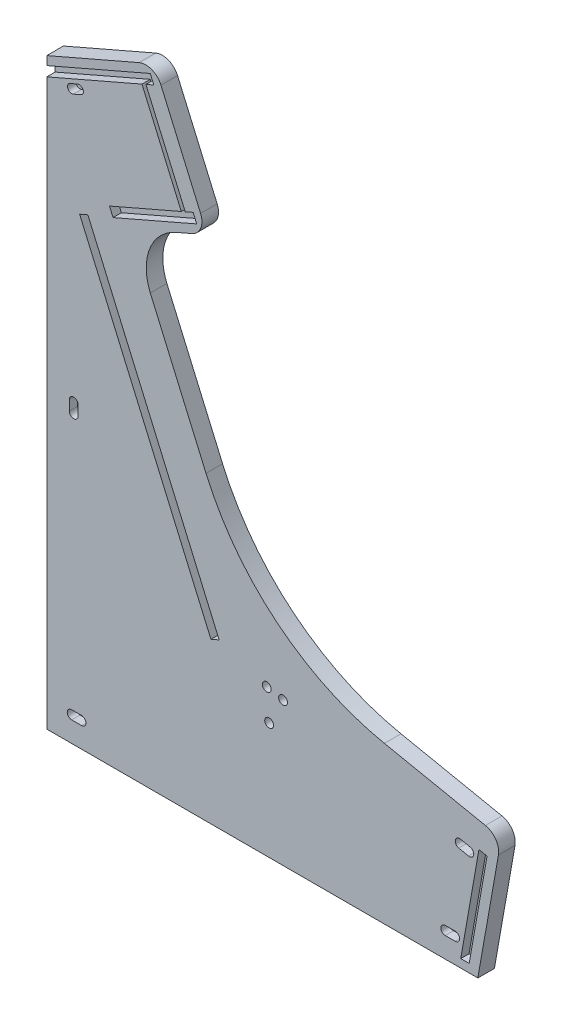
SolidWorks part; units mm, degrees
ref_plane "Alzado" through (0, 0, 0) normal (0, 0, 1) x (1, 0, 0)
ref_plane "Planta" through (0, 0, 0) normal (0, 1, 0) x (1, 0, 0)
ref_plane "Vista lateral" through (0, 0, 0) normal (1, 0, 0) x (0, 0, -1)
sketch "Croquis1" plane through (0, 0, 0) normal (0, 0, 1) x (1, 0, 0)
  line L8 (0, 0) -> (260, 0)
  line L9 (260, 0) -> (274.1062, 80)
  line L10 (274.1062, 80) -> (127.1368, 110)
  line L11 (127.1368, 110) -> (50.509, 286.5431)
  line L12 (50.509, 286.5431) -> (96.7519, 306.6146)
  line L13 (96.7519, 306.6146) -> (64.8993, 380)
  line L14 (64.8993, 380) -> (0, 351.8307)
  line L15 (0, 351.8307) -> (0, 0)
  dimension "D1" = 380
  dimension "D2" = 260
  dimension "D3" = 80
  dimension "D4" = 150
  dimension "D5" = 100
  dimension "D6" = 110
  dimension "D7" = 125
  dimension "D8" = 80
extrude "Saliente-Extruir1" add sketch "Croquis1" along normal blind 10
fillet "Redondeo1" radius 30 1 edges at (50.509, 286.5431, 5)
fillet "Redondeo2" radius 150 1 edges at (127.1368, 110, 5)
fillet "Redondeo3" radius 10 3 edges at (64.8993, 380, 5) (96.7519, 306.6146, 5) (274.1062, 80, 5)
sketch "Croquis2" plane through (0, 0, 10) normal (0, 0, 1) x (1, 0, 0)
  line L0 (39.907, 287.3921) -> (90.176, 309.2111) construction
  line L8 (90.176, 309.2111) -> (88.1852, 313.7977) construction
  line L10 (37.9163, 291.9786) -> (88.1852, 313.7977) construction
  line L11 (0, 340.9294) -> (45.3064, 360.5944) construction
  line L18 (64.2958, 368.8367) -> (62.305, 373.4233) construction
  line L21 (0, 346.3801) -> (62.305, 373.4233) construction
  line L22 (45.3064, 360.5944) -> (64.2958, 368.8367) construction
  line L23 (55.7261, 376.0184) -> (87.5787, 302.6331) construction
  line L24 (68.8809, 370.8268) -> (64.2958, 368.8367) construction
  line L25 (92.7703, 315.7878) -> (88.1852, 313.7977) construction
  line L26 (0, 351.8307) -> (55.7261, 376.0184) construction
  line L30 (39.9867, 287.2086) -> (90.4391, 309.1073)
  line L31 (90.4391, 309.1073) -> (88.2891, 314.0608)
  line L34 (0, 346.5981) -> (0, 340.7114)
  line L35 (37.8366, 292.1621) -> (81.1325, 310.9545)
  line L36 (0, 340.7114) -> (57.4023, 365.6266)
  line L37 (64.5589, 368.7329) -> (62.4088, 373.6864)
  line L38 (0, 346.5981) -> (62.4088, 373.6864)
  line L39 (92.7703, 315.7878) -> (68.8809, 370.8268) construction
  line L40 (39.9867, 287.2086) -> (37.8366, 292.1621)
  line L41 (57.4023, 365.6266) -> (81.1325, 310.9545)
  line L44 (59.7873, 366.6618) -> (83.5175, 311.9897)
  line L45 (59.7873, 366.6618) -> (64.5589, 368.7329)
  line L46 (83.5175, 311.9897) -> (88.2891, 314.0608)
  line L48 (57.3227, 365.81) -> (81.2121, 310.771) construction
  line L49 (59.7077, 366.8453) -> (83.5971, 311.8062) construction
  arc A1 (92.7703, 315.7878) -> (87.5787, 302.6331) centre (83.5971, 311.8062) cw construction
  arc A4 (55.7261, 376.0184) -> (68.8809, 370.8268) centre (59.7077, 366.8453) cw construction
  point P18 (53.3411, 374.9832)
  point P20 (85.1937, 301.5978)
  point P22 (-1.9908, 280.3259)
  point P25 (79.1417, 315.5411)
  dimension "D1" = 10
  dimension "D2" = 55
  dimension "D3" = 4.9984
extrude "Cortar-Extruir1" cut sketch "Croquis2" against normal blind 5
sketch "Croquis3" [suppressed] plane through (0, 0, 0) normal (0, 0, -1) x (-1, 0, 0)
  line L0 (0, 351.8307) -> (-55.7261, 376.0184) construction
  line L10 (0, 346.5981) -> (-62.4088, 373.6864)
  line L12 (-64.5589, 368.7329) -> (-62.4088, 373.6864)
  line L19 (0, 340.7114) -> (-57.4023, 365.6266)
  line L28 (-37.8366, 292.1621) -> (-81.1325, 310.9545)
  line L29 (-92.7703, 315.7878) -> (-88.1852, 313.7977) construction
  line L30 (-47.6793, 361.4064) -> (-64.5589, 368.7329) construction
  line L31 (-68.8809, 370.8268) -> (-64.2958, 368.8367) construction
  line L32 (-55.7261, 376.0184) -> (-87.5787, 302.6331) construction
  line L34 (-45.3064, 360.5944) -> (-64.2958, 368.8367) construction
  line L35 (0, 346.5981) -> (0, 340.7114)
  line L36 (0, 346.3801) -> (-62.305, 373.4233) construction
  line L37 (-64.2958, 368.8367) -> (-62.305, 373.4233) construction
  line L38 (0, 340.9294) -> (-45.3064, 360.5944) construction
  line L39 (-37.9163, 291.9786) -> (-88.1852, 313.7977) construction
  line L40 (-90.176, 309.2111) -> (-88.1852, 313.7977) construction
  line L42 (-39.907, 287.3921) -> (-90.176, 309.2111) construction
  line L45 (-90.4391, 309.1073) -> (-88.2891, 314.0608)
  line L46 (-39.9867, 287.2086) -> (-90.4391, 309.1073)
  line L50 (-71.4095, 306.7343) -> (-88.2891, 314.0608) construction
  line L51 (0.0796, 346.5635) -> (-62.4088, 373.6864) construction
  line L52 (-0.0796, 269.8871) -> (-90.4391, 309.1073) construction
  line L53 (-47.5997, 361.5898) -> (-64.2958, 368.8367) construction
  line L54 (-71.4891, 306.5508) -> (-88.1852, 313.7977) construction
  line L55 (-90.176, 309.2111) -> (-88.1852, 313.7977) construction
  line L56 (-57.4023, 365.6266) -> (-81.1325, 310.9545)
  line L57 (-59.7873, 366.6618) -> (-64.5589, 368.7329)
  line L58 (-53.3411, 374.9832) -> (-85.1937, 301.5978) construction
  line L59 (-83.5175, 311.9897) -> (-88.2891, 314.0608)
  line L60 (-83.5175, 311.9897) -> (-59.7873, 366.6618)
  line L61 (-39.9867, 287.2086) -> (-37.8366, 292.1621)
  line L63 (0, 270.0706) -> (-90.176, 309.2111) construction
  arc A0 (-55.7261, 376.0184) -> (-68.8809, 370.8268) centre (-59.7077, 366.8453) ccw construction
  arc A1 (-92.7703, 315.7878) -> (-87.5787, 302.6331) centre (-83.5971, 311.8062) ccw construction
  point P10 (0.0796, 275.7047)
  point P11 (-69.1162, 305.7389)
  dimension "D1" = 0.2
  dimension "D2" = 2.6
  dimension "D4" = 4.9984
  dimension "D3" = 55
extrude "Cortar-Extruir2" [suppressed] cut sketch "Croquis3" against normal blind 5
sketch "Croquis4" plane through (0, 0, 10) normal (0, 0, 1) x (1, 0, 0)
  line L0 (268.3369, 76.0745) -> (121.3675, 106.0745) construction
  line L1 (121.3675, 106.0745) -> (119.3675, 96.2766) construction
  line L2 (268.3369, 76.0745) -> (266.3369, 66.2766) construction
  line L3 (266.3369, 66.2766) -> (119.3675, 96.2766) construction
  line L4 (260, 0) -> (272.1806, 69.3941) construction
  line L5 (266.3369, 66.2766) -> (101.9099, 66.2766) construction
  line L6 (267.3369, 71.1756) -> (257.5389, 73.1756) construction
  line L7 (257.5389, 73.1756) -> (256.1307, 66.2766) construction
  line L8 (131.1654, 104.0745) -> (123.45, 66.2766) construction
  line L9 (131.1654, 104.0745) -> (129.1654, 94.2766) construction
  line L10 (254.7859, 5) -> (265.5692, 66.4333)
  line L12 (87.7908, 178.0453) -> (54.1979, 255.4402)
  line L13 (120.6196, 102.4108) -> (54.1979, 255.4402) construction
  line L17 (249.7095, 5) -> (260.6683, 67.4337)
  line L18 (249.8612, 5.8644) -> (260.6444, 67.2977) construction
  line L19 (118.3675, 91.3776) -> (132.7094, 88.4501) construction
  line L20 (119.3675, 96.2766) -> (118.3675, 91.3776) construction
  line L21 (249.5225, 67.1478) -> (255.4012, 65.9474) construction
  line L22 (137.6083, 87.4501) -> (134.1093, 70.3081) construction
  line L23 (254.0903, 1.0373) -> (266.2709, 70.4314) construction
  line L24 (0, 5) -> (260, 5)
  line L25 (249.7095, 5) -> (254.7859, 5)
  line L26 (260.6683, 67.4337) -> (265.5692, 66.4333)
  line L27 (248.5222, 62.2489) -> (254.4009, 61.0485) construction
  line L28 (240.3347, 17.65) -> (246.3347, 17.65)
  line L29 (254.901, 63.4979) -> (117.3877, 91.5777) construction
  line L30 (249.5525, 67.2947) -> (255.4312, 66.0943)
  line L31 (240.3347, 12.35) -> (246.3347, 12.35)
  line L32 (248.4922, 62.1019) -> (254.3708, 60.9015)
  line L33 (0, 351.8307) -> (0, 0) construction
  line L34 (15, 17.65) -> (21, 17.65)
  line L35 (0, 15) -> (260, 15)
  line L36 (15, 15) -> (251.4647, 15) construction
  line L37 (15, 340.7114) -> (15, 0)
  line L38 (15, 341.9894) -> (15, 15) construction
  line L39 (15, 12.35) -> (21, 12.35)
  line L40 (99.1156, 96.6994) -> (119.3675, 96.2766) construction
  line L41 (119.3675, 96.2766) -> (119.2966, 105.4588) construction
  line L42 (119.2966, 105.4588) -> (121.1313, 106.2552) construction
  line L43 (121.1313, 106.2552) -> (119.3675, 96.2766) construction
  line L44 (99.1156, 96.6994) -> (103.7022, 98.6902) construction
  line L45 (99.1156, 96.6994) -> (20.0814, 278.7868) construction
  line L46 (20.0814, 278.7868) -> (24.668, 280.7776) construction
  line L47 (24.668, 280.7776) -> (103.7022, 98.6902) construction
  line L48 (99.0118, 96.4363) -> (19.8183, 278.8907)
  line L49 (19.8183, 278.8907) -> (24.7718, 281.0407)
  line L50 (24.7718, 281.0407) -> (103.9653, 98.5863)
  line L51 (99.0118, 96.4363) -> (103.9653, 98.5863)
  line L52 (0, 175.9154) -> (16.25, 175.9154) construction
  line L53 (16.25, 178.9154) -> (16.25, 172.9154) construction
  line L54 (13.6, 178.9154) -> (13.6, 172.9154)
  line L55 (18.9, 178.9154) -> (18.9, 172.9154)
  line L56 (0, 340.7114) -> (57.4023, 365.6266) construction
  line L57 (15, 341.9894) -> (55.4532, 359.5479) construction
  line L60 (14.0046, 344.2827) -> (18.5912, 346.2735)
  line L62 (15.9954, 339.6961) -> (20.582, 341.6869)
  arc A0 (272.1806, 69.3941) -> (264.5676, 81.9471) centre (262.5676, 72.1491) ccw construction
  arc A3 (254.4009, 61.0485) -> (255.4012, 65.9474) centre (254.901, 63.4979) ccw construction
  arc A4 (249.5225, 67.1478) -> (248.5222, 62.2489) centre (249.0223, 64.6983) ccw construction
  arc A5 (254.3708, 60.9015) -> (255.4312, 66.0943) centre (254.901, 63.4979) ccw
  circle A6 centre (132.7094, 88.4501) radius 2.65
  circle A7 centre (142.5073, 86.4501) radius 2.65
  circle A8 centre (134.1093, 70.3081) radius 2.65
  arc A9 (249.5525, 67.2947) -> (248.4922, 62.1019) centre (249.0223, 64.6983) ccw
  arc A10 (246.3347, 12.35) -> (246.3347, 17.65) centre (246.3347, 15) ccw
  arc A11 (240.3347, 17.65) -> (240.3347, 12.35) centre (240.3347, 15) ccw
  arc A12 (15, 17.65) -> (15, 12.35) centre (15, 15) ccw
  arc A13 (21, 12.35) -> (21, 17.65) centre (21, 15) ccw
  arc A14 (18.9, 178.9154) -> (13.6, 178.9154) centre (16.25, 178.9154) ccw
  arc A15 (13.6, 172.9154) -> (18.9, 172.9154) centre (16.25, 172.9154) ccw
  arc A16 (14.0046, 344.2827) -> (15.9954, 339.6961) centre (15, 341.9894) ccw
  arc A17 (20.582, 341.6869) -> (18.5912, 346.2735) centre (19.5866, 343.9802) ccw
  point P36 (265.3369, 61.3776)
  point P38 (244.7848, 5.8644)
  point P39 (255.7436, 68.2981)
  point P86 (5, 351.8307)
  point P88 (5, 0)
  point P91 (16.25, 175.9154)
  dimension "D11" = 5.3
  dimension "D13" = 6
  dimension "D12" = 5.3
  dimension "D20" = 5.3
  dimension "D22" = 16.25
  dimension "D24" = 2.65
  dimension "D27" = 2.5
  dimension "D1" = 10
  dimension "D4" = 11.537
  dimension "D5" = 6
  dimension "D6" = 14.6376
  dimension "D7" = 5
  dimension "D8" = 10
  dimension "D9" = 5
  dimension "D10" = 17.4955
  dimension "D16" = 6
  dimension "D17" = 5.13
  dimension "D19" = 6
  dimension "D21" = 0.2
  dimension "D23" = 6
  dimension "D28" = 5
  dimension "D25" = 4.8
  dimension "D2" = 10
  dimension "D3" = 9
  dimension "D14" = 0.15
  dimension "D15" = 15
  dimension "D18" = 15
extrude "Cortar-Extruir3" cut sketch "Croquis4" against normal blind 5
